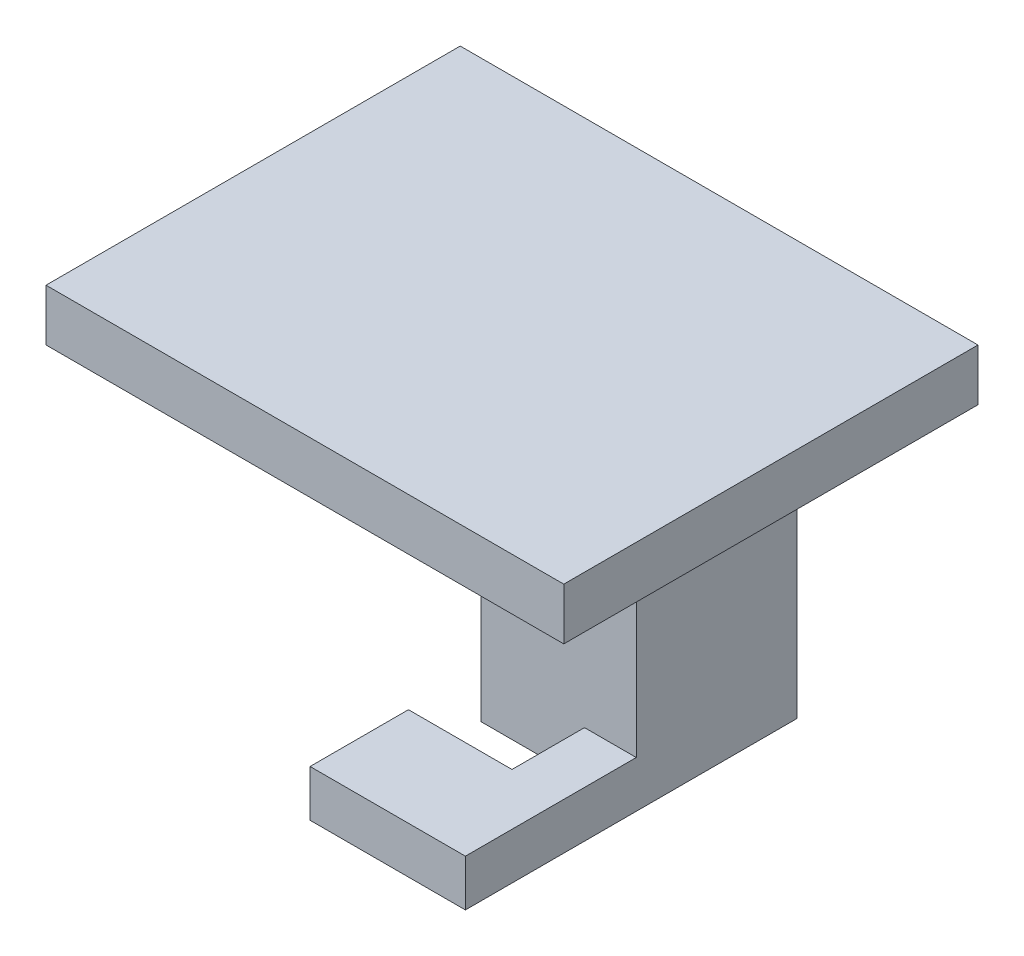
SolidWorks part; units mm, degrees
ref_plane "Front Plane" through (0, 0, 0) normal (0, 0, 1) x (1, 0, 0)
ref_plane "Top Plane" through (0, 0, 0) normal (0, 1, 0) x (1, 0, 0)
ref_plane "Right Plane" through (0, 0, 0) normal (1, 0, 0) x (0, 0, -1)
sketch "Sketch1" plane through (0, 0, 0) normal (0, 0, 1) x (1, 0, 0)
  line L0 (-7.5, -17.5) -> (7.5, 17.5) construction
  line L1 (-7.5, 17.5) -> (7.5, 17.5)
  line L2 (-7.5, 17.5) -> (-7.5, -17.5)
  line L3 (-7.5, -17.5) -> (7.5, -17.5)
  line L4 (7.5, 17.5) -> (7.5, -17.5)
  line L5 (-7.5, 17.5) -> (7.5, -17.5) construction
  point P4 (0, 0)
  dimension "D1" = 35
  dimension "D2" = 15
extrude "Boss-Extrude1" add sketch "Sketch1" along normal blind 32
sketch "Sketch4" plane through (0, 0, 32) normal (0, 0, 1) x (1, 0, 0)
  line L2 (-7.5, 10) -> (-7.5, -13)
  line L4 (7.5, 10) -> (7.5, -13)
  line L5 (7.5, -17.5) -> (7.5, 17.5) construction
  line L6 (7.5, 10) -> (-7.5, -13) construction
  line L7 (-7.5, 17.5) -> (-7.5, -17.5) construction
  line L8 (-7.5, -17.5) -> (7.5, -17.5) construction
  line L10 (7.5, 10) -> (-7.5, -13) construction
  line L11 (-7.5, 10) -> (7.5, 10)
  line L12 (-7.5, 10) -> (-7.5, -13)
  line L13 (-7.5, -13) -> (7.5, -13)
  line L14 (7.5, 10) -> (7.5, -13)
  line L15 (7.5, -13) -> (-7.5, 10) construction
  line L16 (7.5, -13) -> (-7.5, -13) construction
  point P4 (0, 0)
  point P10 (0, -1.5)
  point P12 (0, -1.5)
  point P14 (-1.5826, -13)
  point P15 (0, 0)
  point P19 (0, -13)
  dimension "D1" = 23
  dimension "D2" = 4.5
extrude "Cut-Extrude2" cut sketch "Sketch4" against normal blind 16.5 contours L2 L13 L4 L11
sketch "Sketch7" plane through (0, 0, 0) normal (0, 0, -1) x (-1, 0, 0)
  line L0 (7.5, -17.5) -> (-7.5, -17.5) construction
  circle A0 centre (0, -6.4) radius 2.5
  dimension "D1" = 5
  dimension "D2" = 11.1
extrude "Boss-Extrude2" add sketch "Sketch7" along normal blind 3
sketch "Sketch9" plane through (0, 17.5, 0) normal (0, 1, 0) x (1, 0, 0)
  line L0 (7.5, 0) -> (-7.5, 0) construction
  line L1 (-25, 0) -> (25, 0)
  line L2 (-25, 0) -> (-25, -40)
  line L3 (-25, -40) -> (25, -40)
  line L4 (25, 0) -> (25, -40)
  point P6 (0, 0)
  dimension "D1" = 40
  dimension "D2" = 50
extrude "Boss-Extrude3" add sketch "Sketch9" along normal blind 5
sketch "Sketch10" plane through (-7.5, 0, 0) normal (-1, 0, 0) x (0, 0, 1)
  line L0 (32, -17.5) -> (0, -17.5) construction
  line L1 (15.5, -17.5) -> (22.5, -17.5)
  line L2 (15.5, -17.5) -> (15.5, -13)
  line L3 (15.5, -13) -> (22.5, -13)
  line L4 (22.5, -17.5) -> (22.5, -13)
  line L5 (15.5, -13) -> (32, -13) construction
  line L6 (15.5, 10) -> (15.5, -13) construction
  dimension "D1" = 7
extrude "Cut-Extrude3" cut sketch "Sketch10" against normal blind 10
